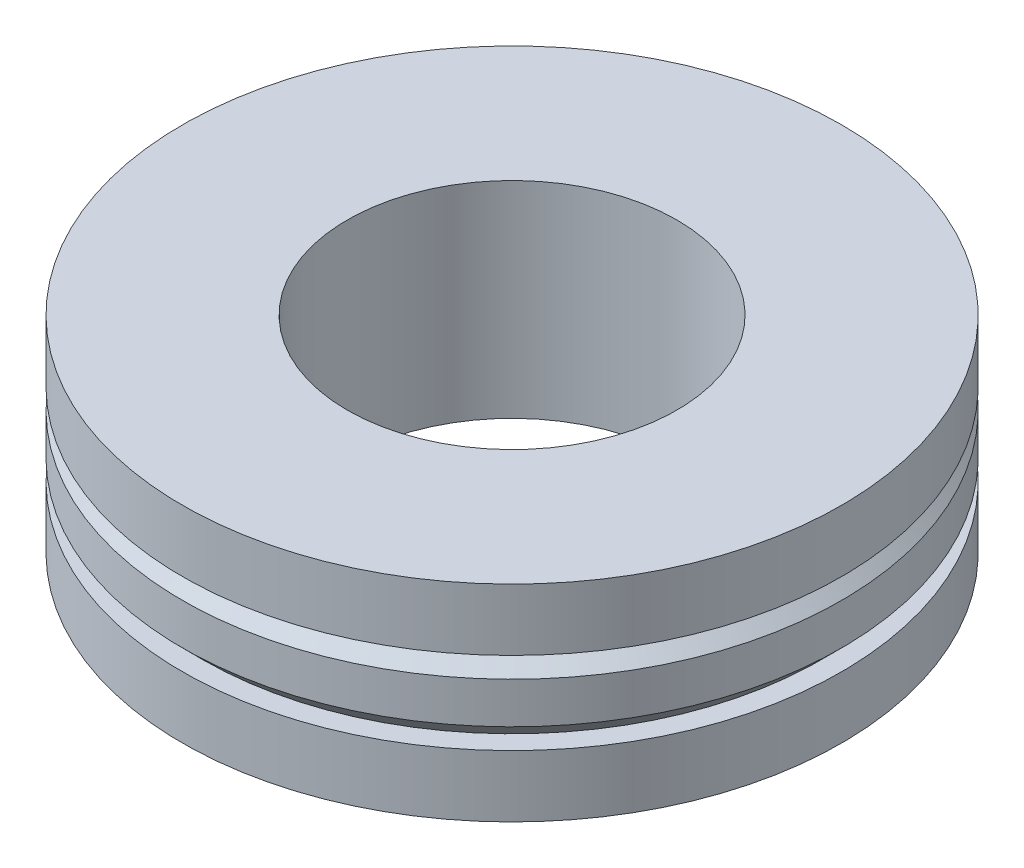
SolidWorks part; units mm, degrees
ref_plane "前视基准面" through (0, 0, 0) normal (0, 0, 1) x (1, 0, 0)
ref_plane "上视基准面" through (0, 0, 0) normal (0, 1, 0) x (1, 0, 0)
ref_plane "右视基准面" through (0, 0, 0) normal (1, 0, 0) x (0, 0, -1)
sketch "草图1" plane through (0, 0, 0) normal (0, 0, 1) x (1, 0, 0)
  line L0 (-112, 5) -> (-116, 5)
  line L1 (-116, 5) -> (-116, 0)
  line L2 (-116, 0) -> (-112, 0)
  line L3 (-112, 0) -> (-112, 1.5)
  line L4 (-112, 1.5) -> (-112.5, 1.5)
  line L5 (-112.5, 1.5) -> (-112, 2)
  line L6 (-112, 2) -> (-112, 3)
  line L7 (-112, 3) -> (-112.5, 3.5)
  line L8 (-112.5, 3.5) -> (-112, 3.5)
  line L9 (-112, 3.5) -> (-112, 5)
  line L10 (-120, 5) -> (-120, 0) construction
revolve "旋转1" add sketch "草图1" angle 360 about L10
